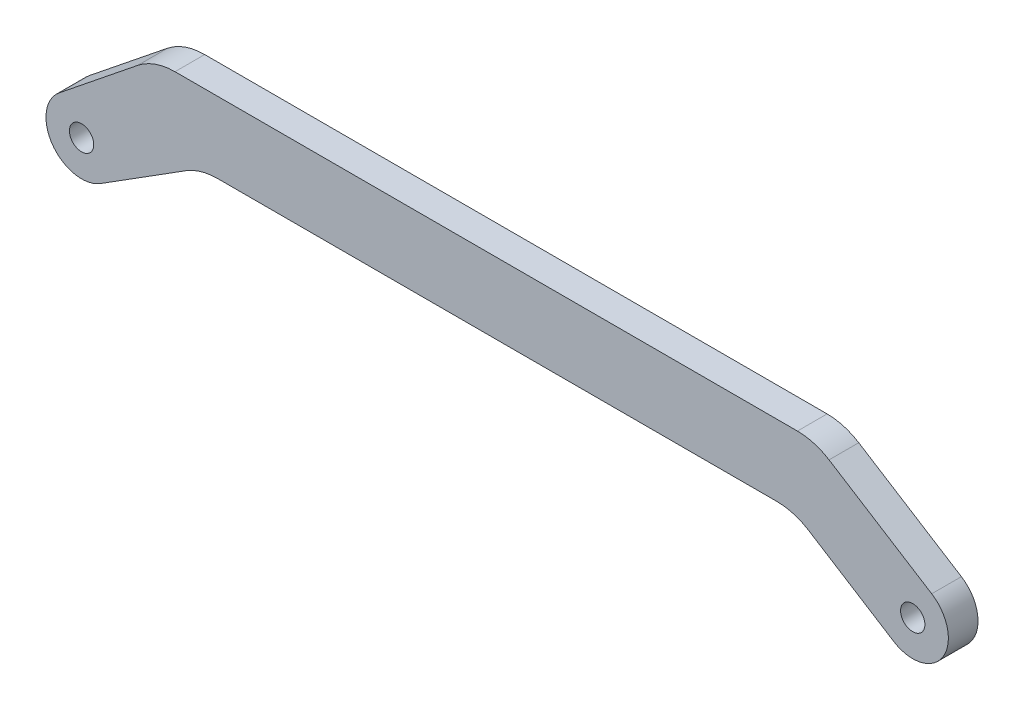
SolidWorks part; units mm, degrees
material "Acrílico (Impacto medio-alto)"
ref_plane "Piano frontale" through (0, 0, 0) normal (0, 0, 1) x (1, 0, 0)
ref_plane "Piano superiore" through (0, 0, 0) normal (0, 1, 0) x (1, 0, 0)
ref_plane "Piano destro" through (0, 0, 0) normal (1, 0, 0) x (0, 0, -1)
sketch "Schizzo1" plane through (0, 0, 0) normal (0, 0, 1) x (1, 0, 0)
  line L0 (0, 0) -> (2.05, 0) construction
  line L1 (0, 0) -> (2.05, 0) construction
  line L2 (-3.757, 4.6781) -> (9.4748, 15.3047)
  line L3 (15.7365, 17.5078) -> (120.5774, 17.5078)
  line L4 (122.4429, 3.9689) -> (136.8019, -5.0767)
  line L5 (125.9075, 15.9689) -> (143.1981, 5.0767)
  line L7 (17.5571, 3.9689) -> (3.1981, -5.0767)
  line L8 (22.8872, 5.5078) -> (117.1128, 5.5078)
  line L11 (0, 0) -> (137.95, 0) construction
  circle A0 centre (0, 0) radius 2.05
  circle A1 centre (140, 0) radius 2.05
  arc A2 (136.8019, -5.0767) -> (143.1981, 5.0767) centre (140, 0) ccw
  arc A3 (122.4429, 3.9689) -> (117.1128, 5.5078) centre (117.1128, -4.4922) ccw
  arc A4 (120.5774, 17.5078) -> (125.9075, 15.9689) centre (120.5774, 7.5078) cw
  arc A5 (-3.757, 4.6781) -> (3.1981, -5.0767) centre (0, 0) ccw
  arc A6 (17.5571, 3.9689) -> (22.8872, 5.5078) centre (22.8872, -4.4922) cw
  arc A7 (9.4748, 15.3047) -> (15.7365, 17.5078) centre (15.7365, 7.5078) cw
  point P10 (17.2528, 15)
  point P11 (20, 5.5078)
  point P15 (153.6285, 15)
  point P17 (120, 5.5078)
  point P18 (151.4002, 3)
  point P21 (123.4646, 17.5078)
  point P31 (12.2181, 17.5078)
  dimension "D1" = 4.1
  dimension "D4" = 12
  dimension "D5" = 12
  dimension "D8" = 20
  dimension "D10" = 10
  dimension "D3" = 140
  dimension "D7" = 12
  dimension "D6" = 20
  dimension "D9" = 111.2466
extrude "Estrusione-Estrusione1" add sketch "Schizzo1" along normal blind 5
